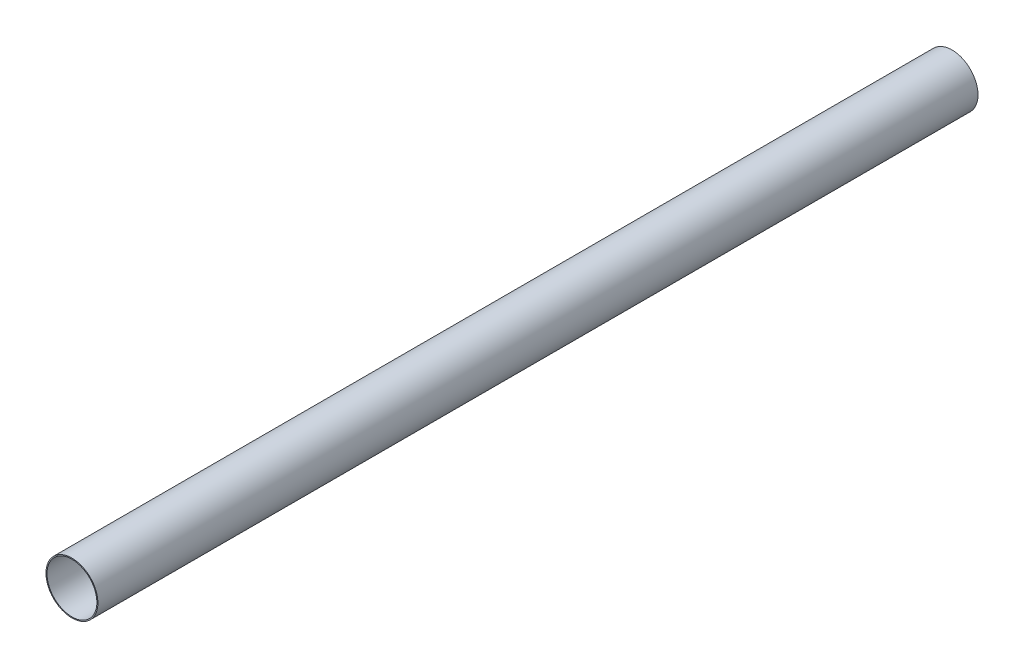
SolidWorks part; units mm, degrees
ref_plane "Front" through (0, 0, 0) normal (0, 0, 1) x (1, 0, 0)
ref_plane "Top" through (0, 0, 0) normal (0, 1, 0) x (1, 0, 0)
ref_plane "Side" through (0, 0, 0) normal (1, 0, 0) x (0, 0, -1)
sketch "PipeSketch" plane through (0, 0, 0) normal (0, 0, 1) x (1, 0, 0)
  circle A0 centre (0, 0) radius 161.925
  circle A1 centre (0, 0) radius 155.575
  dimension "OuterDiameter" = 323.85
  dimension "InnerDiameter" = 311.15
extrude "Extrusion" add sketch "PipeSketch" along normal blind 5486.4
sketch "FilterSketch" plane through (0, 0, 0) normal (0, 0, 1) x (1, 0, 0)
  circle A0 centre (0, 0) radius 152.4 construction
  dimension "NominalDiameter" = 304.8
